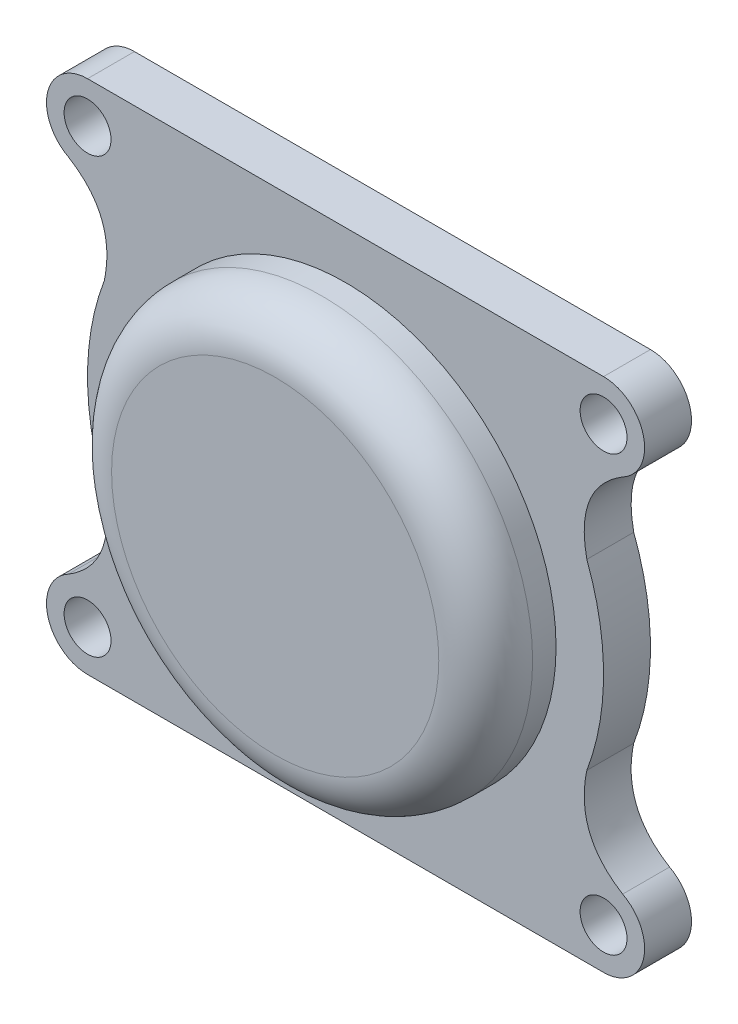
SolidWorks part; units mm, degrees
ref_plane "Front Plane" through (0, 0, 0) normal (0, 0, 1) x (1, 0, 0)
ref_plane "Top Plane" through (0, 0, 0) normal (0, 1, 0) x (1, 0, 0)
ref_plane "Right Plane" through (0, 0, 0) normal (1, 0, 0) x (0, 0, -1)
sketch "Sketch1" plane through (0, 0, 0) normal (0, 0, 1) x (1, 0, 0)
  line L0 (-10.8666, -11.4001) -> (11.1334, -11.4001)
  line L1 (11.1334, 10.5999) -> (-10.8666, 10.5999)
  circle A0 centre (-10.8666, -9.6501) radius 1
  arc A1 (-10.8666, 10.5999) -> (-11.6822, 7.3015) centre (-10.8666, 8.8499) ccw
  arc A2 (-10.1541, 3.4947) -> (-10.1541, -4.2948) centre (0.1334, -0.4001) ccw
  arc A3 (-11.6822, -8.1017) -> (-10.8666, -11.4001) centre (-10.8666, -9.6501) ccw
  arc A4 (11.1334, -11.4001) -> (11.9489, -8.1017) centre (11.1334, -9.6501) ccw
  arc A5 (10.4208, -4.2948) -> (10.4208, 3.4947) centre (0.1334, -0.4001) ccw
  arc A6 (11.9489, 7.3015) -> (11.1334, 10.5999) centre (11.1334, 8.8499) ccw
  circle A7 centre (11.1334, -9.6501) radius 1
  circle A8 centre (-10.8666, 8.8499) radius 1
  circle A9 centre (11.1334, 8.8499) radius 1
  circle A10 centre (0.1334, -0.4001) radius 7.975
  parabola Q0 (-11.6822, 7.3015) -> (-10.1541, 3.4947) focus (-11.6493, 5.2896) apex (-10.3607, 5.9293)
  parabola Q1 (-10.1541, -4.2948) -> (-11.6822, -8.1017) focus (-11.6493, -6.0898) apex (-10.3607, -6.7295)
  parabola Q2 (11.9489, -8.1017) -> (10.4208, -4.2948) focus (11.9161, -6.0898) apex (10.6274, -6.7295)
  parabola Q3 (10.4208, 3.4947) -> (11.9489, 7.3015) focus (11.9161, 5.2896) apex (10.6274, 5.9293)
extrude "Boss-Extrude1" add sketch "Sketch1" along normal blind 2
sketch "Sketch2" plane through (0, 0, 2) normal (0, 0, 1) x (1, 0, 0)
  circle A0 centre (0.1334, -0.4001) radius 7.975 construction
  circle A1 centre (0.1334, -0.4001) radius 7.975
  circle A2 centre (0.1334, -0.4001) radius 8.975
  dimension "D1" = 1
extrude "Boss-Extrude2" add sketch "Sketch2" along normal blind 2
sketch "Sketch3" plane through (0, 0, 4) normal (0, 0, 1) x (1, 0, 0)
  circle A0 centre (0.1334, -0.4001) radius 8.975 construction
  circle A1 centre (0.1334, -0.4001) radius 8.975
extrude "Boss-Extrude3" add sketch "Sketch3" along normal blind 1
fillet "Fillet1" radius 2 2 edges at (9.1084, -0.4001, 5) (8.1084, -0.4001, 4)
